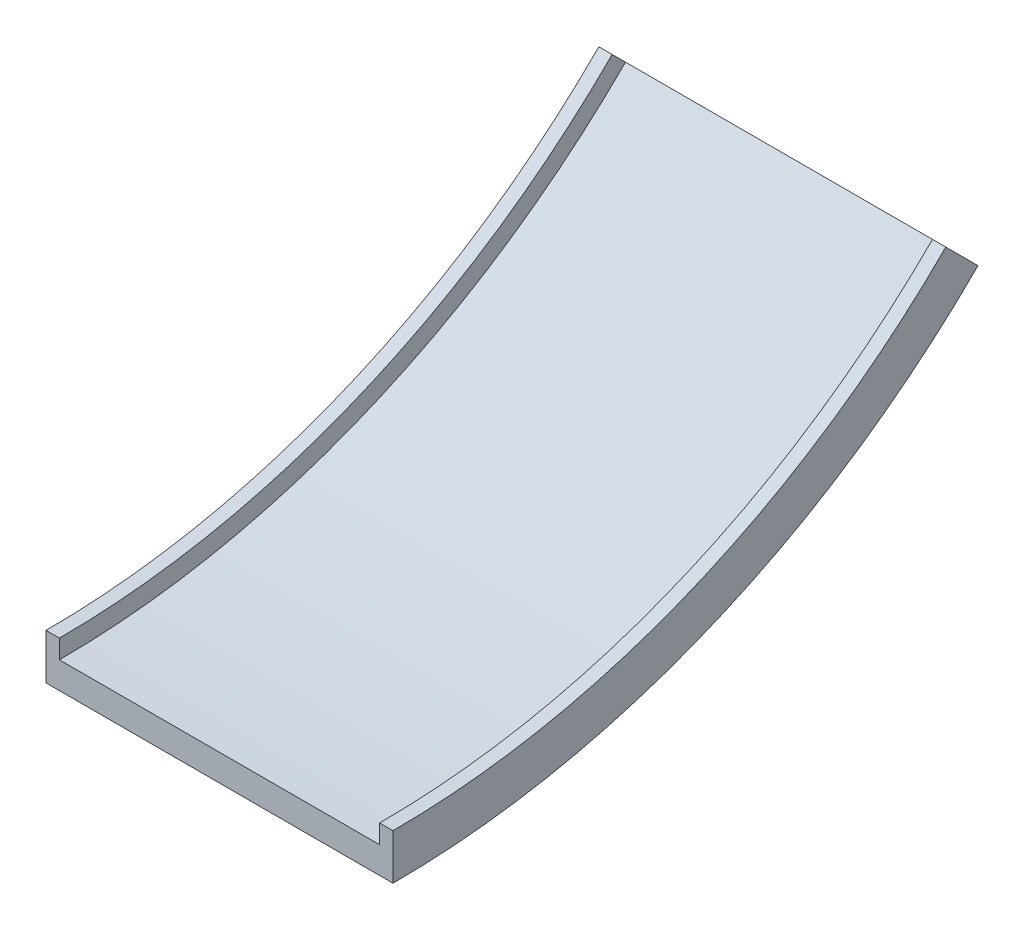
SolidWorks part; units mm, degrees
ref_plane "Front Plane" through (0, 0, 0) normal (0, 0, 1) x (1, 0, 0)
ref_plane "Top Plane" through (0, 0, 0) normal (0, 1, 0) x (1, 0, 0)
ref_plane "Right Plane" through (0, 0, 0) normal (1, 0, 0) x (0, 0, -1)
sketch "Sketch1" plane through (0, 0, 0) normal (0, 0, 1) x (1, 0, 0)
  line L0 (0, 0) -> (25, 0)
  line L1 (25, 0) -> (25, -35.2361)
  line L2 (25, -35.2361) -> (625, -35.2361)
  line L3 (625, -35.2361) -> (625, 0)
  line L4 (625, 0) -> (650, 0)
  line L5 (650, 0) -> (650, -85.2361)
  line L6 (650, -85.2361) -> (0, -85.2361)
  line L7 (0, -85.2361) -> (0, 0)
  line L8 (0, 1464.7639) -> (650, 1464.7639)
  dimension "D1" = 25
  dimension "D2" = 35.2361
  dimension "D3" = 650
  dimension "D4" = 50
  dimension "D5" = 1500
revolve "Revolve1" add sketch "Sketch1" angle 45 about L8
